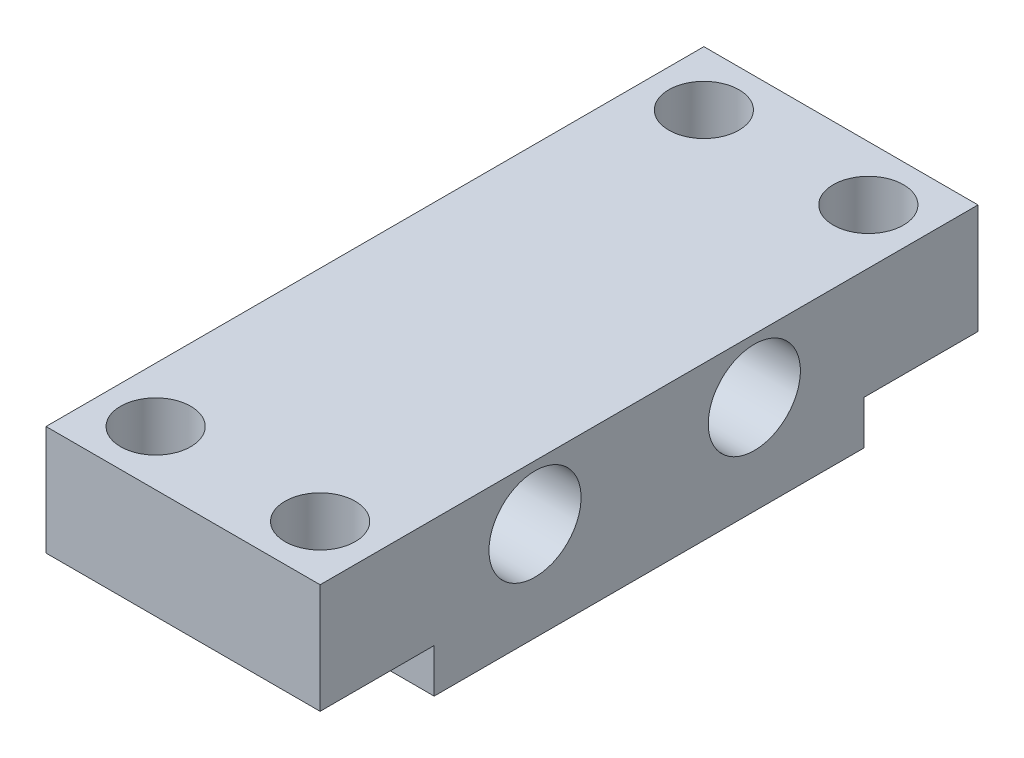
SolidWorks part; units mm, degrees
ref_plane "Front Plane" through (0, 0, 0) normal (0, 0, 1) x (1, 0, 0)
ref_plane "Top Plane" through (0, 0, 0) normal (0, 1, 0) x (1, 0, 0)
ref_plane "Right Plane" through (0, 0, 0) normal (1, 0, 0) x (0, 0, -1)
sketch "Sketch1" plane through (0, 0, 0) normal (0, 1, 0) x (1, 0, 0)
  line L1 (0, 0) -> (12.5, 0)
  line L2 (0, 0) -> (0, 30)
  line L3 (0, 30) -> (12.5, 30)
  line L4 (12.5, 0) -> (12.5, 30)
  dimension "D1" = 30
  dimension "D2" = 12.5
extrude "Boss-Extrude1" add sketch "Sketch1" along normal blind 5
sketch "Sketch2" plane through (0, 0, 0) normal (0, -1, 0) x (1, 0, 0)
  line L0 (0, -30) -> (0, 0) construction
  line L1 (0, -5.2) -> (12.5, -5.2)
  line L2 (0, -5.2) -> (0, -24.8)
  line L3 (0, -24.8) -> (12.5, -24.8)
  line L4 (12.5, -5.2) -> (12.5, -24.8)
  line L5 (12.5, 0) -> (12.5, -30) construction
  line L6 (0, 0) -> (12.5, 0) construction
  line L7 (12.5, -30) -> (0, -30) construction
  dimension "D1" = 5.2
  dimension "D2" = 5.2
extrude "Boss-Extrude2" add sketch "Sketch2" along normal blind 2
sketch "Sketch3" plane through (0, 0, 0) normal (-1, 0, 0) x (0, 0, 1)
  line L0 (-24.8, -2) -> (-24.8, 0) construction
  line L1 (-5.2, -2) -> (-24.8, -2) construction
  circle A0 centre (-19.8, 2.5) radius 2.1
  circle A1 centre (-9.8, 2.5) radius 2.1
  dimension "D1" = 4.2
  dimension "D2" = 4.2
  dimension "D3" = 5
  dimension "D4" = 4.5
  dimension "D5" = 4.5
  dimension "D6" = 10
extrude "Cut-Extrude1" cut sketch "Sketch3" against normal blind 15
sketch "Sketch4" plane through (0, 5, 0) normal (0, 1, 0) x (1, 0, 0)
  line L0 (0, 0) -> (12.5, 0) construction
  line L1 (0, 30) -> (0, 0) construction
  line L2 (12.5, 30) -> (0, 30) construction
  circle A0 centre (2.5, 27.5) radius 1.6
  circle A1 centre (2.5, 2.5) radius 1.6
  dimension "D1" = 3.2
  dimension "D2" = 3.2
  dimension "D3" = 2.5
  dimension "D4" = 2.5
  dimension "D5" = 2.5
  dimension "D6" = 2.5
extrude "Cut-Extrude2" cut sketch "Sketch4" against normal blind 10
pattern_linear "LPattern1" count 2 spacing 7.5 along (1, 0, 0) of "Cut-Extrude2"
